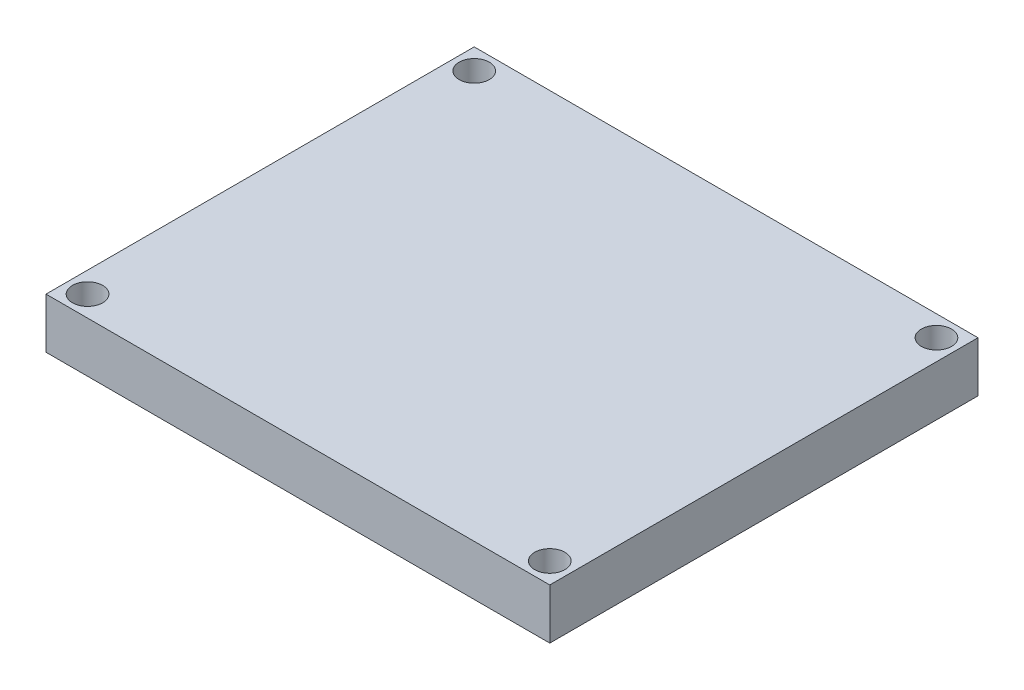
SolidWorks part; units mm, degrees
material "ABS"
ref_plane "Front Plane" through (0, 0, 0) normal (0, 0, 1) x (1, 0, 0)
ref_plane "Top Plane" through (0, 0, 0) normal (0, 1, 0) x (1, 0, 0)
ref_plane "Right Plane" through (0, 0, 0) normal (1, 0, 0) x (0, 0, -1)
sketch "Sketch1" plane through (0, 0, 0) normal (0, 1, 0) x (1, 0, 0)
  line L1 (-25.4, -21.59) -> (25.4, -21.59)
  line L2 (-25.4, -21.59) -> (-25.4, 21.59)
  line L3 (-25.4, 21.59) -> (25.4, 21.59)
  line L4 (25.4, -21.59) -> (25.4, 21.59)
  line L5 (-25.4, -21.59) -> (25.4, 21.59) construction
  line L6 (-25.4, 21.59) -> (25.4, -21.59) construction
  circle A0 centre (-23.3045, 19.4945) radius 1.524
  circle A1 centre (23.3045, 19.4945) radius 1.524
  circle A2 centre (-23.3045, -19.4945) radius 1.524
  circle A3 centre (23.3045, -19.4945) radius 1.524
  point P0 (0, 0)
  dimension "D3" = 3.048
  dimension "D1" = 50.8
  dimension "D2" = 43.18
  dimension "D4" = 2.0955
  dimension "D5" = 2.0955
  dimension "D6" = 2.0955
  dimension "D7" = 2.0955
  dimension "D8" = 2.0955
  dimension "D9" = 2.0955
  dimension "D10" = 2.0955
  dimension "D11" = 2.0955
sketch "Sketch2" plane through (0, 0, 0) normal (0, 1, 0) x (1, 0, 0)
extrude "Boss-Extrude1" add sketch "Sketch1" along normal blind 5.08
